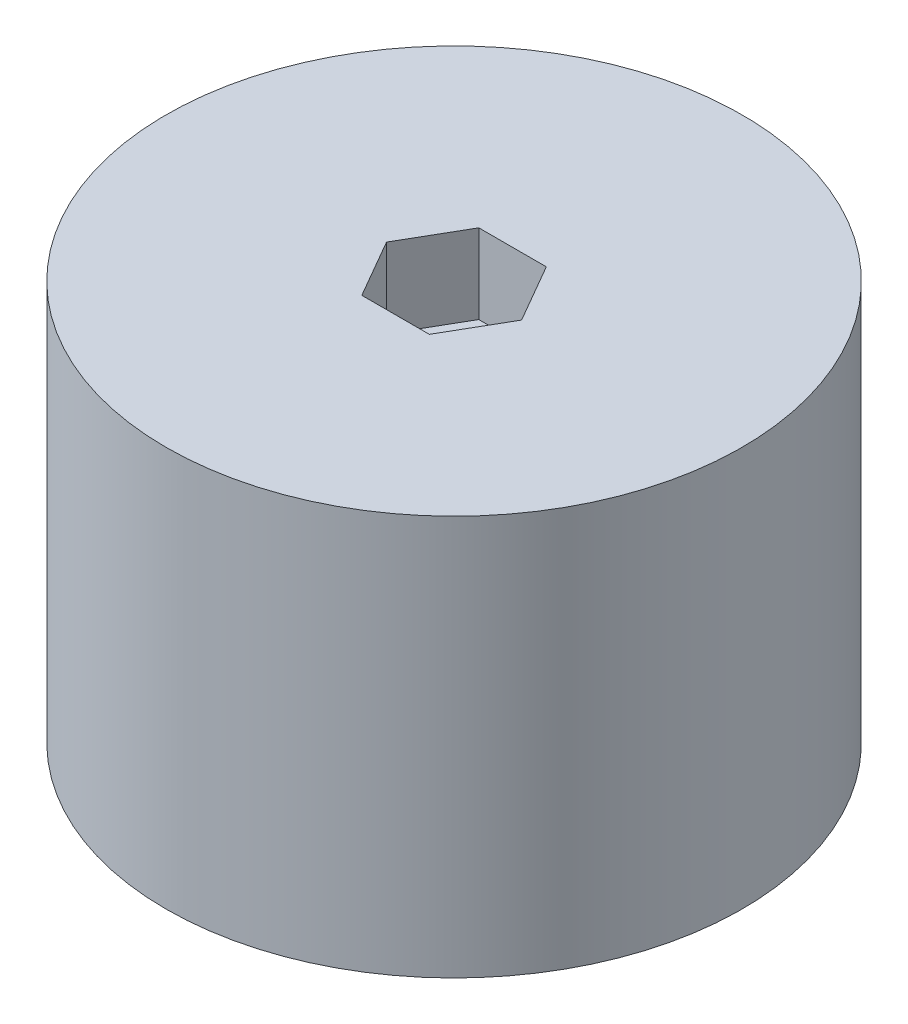
SolidWorks part; units mm, degrees
ref_plane "Front Plane" through (0, 0, 0) normal (0, 0, 1) x (1, 0, 0)
ref_plane "Top Plane" through (0, 0, 0) normal (0, 1, 0) x (1, 0, 0)
ref_plane "Right Plane" through (0, 0, 0) normal (1, 0, 0) x (0, 0, -1)
sketch "Sketch1" plane through (0, 0, 0) normal (0, 1, 0) x (1, 0, 0)
  circle A0 centre (0, 0) radius 21.75
  circle A1 centre (0, 0) radius 3
  dimension "D1" = 43.5
  dimension "D2" = 6
extrude "Boss-Extrude1" add sketch "Sketch1" along normal blind 30.2
sketch "Sketch2" plane through (0, 30.2, 0) normal (0, 1, 0) x (1, 0, 0)
  line L1 (5.1, 0) -> (2.55, 4.4167)
  line L2 (2.55, 4.4167) -> (-2.55, 4.4167)
  line L3 (-2.55, 4.4167) -> (-5.1, 0)
  line L4 (-5.1, 0) -> (-2.55, -4.4167)
  line L5 (-2.55, -4.4167) -> (2.55, -4.4167)
  line L6 (2.55, -4.4167) -> (5.1, 0)
  circle A0 centre (0, 0) radius 4.4167 construction
  dimension "D1" = 5.1
extrude "Cut-Extrude1" cut sketch "Sketch2" against normal blind 6
